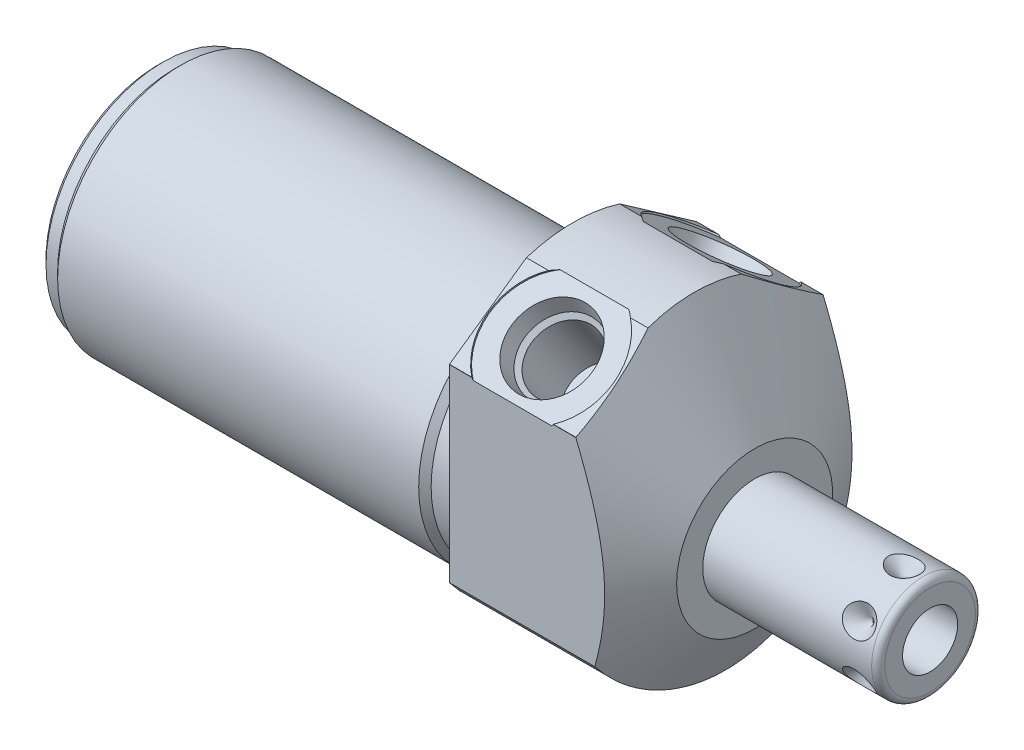
SolidWorks part; units mm, degrees
material "Alloy Steel"
ref_plane "Front Plane" through (0, 0, 0) normal (0, 0, 1) x (1, 0, 0)
ref_plane "Top Plane" through (0, 0, 0) normal (0, 1, 0) x (1, 0, 0)
ref_plane "Right Plane" through (0, 0, 0) normal (1, 0, 0) x (0, 0, -1)
ref_plane "Plane1" through (0, 0, 0) normal (1, 0, 0) x (0, 0, -1)
sketch "Sketch1" plane through (0, 0, 0) normal (1, 0, 0) x (0, 0, -1)
  circle A0 centre (0, 0) radius 23.8125
  dimension "D1" = 47.625
extrude "Extrude1" add sketch "Sketch1" along normal blind 27.7876 and the other way blind 63.5
ref_plane "Plane2" through (0, 0, 0) normal (1, 0, 0) x (0, 0, -1)
sketch "Sketch2" plane through (0, 0, 0) normal (1, 0, 0) x (0, 0, -1)
  line L0 (-20.7455, -4.191) -> (20.7455, -4.191) construction
  circle A0 centre (0, -4.191) radius 18.8595
  circle A1 centre (0, 0) radius 23.8125 construction
  circle A2 centre (0, 0) radius 23.8125
  dimension "D2" = 37.719
  dimension "D1" = 4.191
extrude "Cut-Extrude1" cut sketch "Sketch2" against normal up to next
ref_plane "Plane4" through (0, 0, 0) normal (-1, 0, 0) x (0, 0, 1)
sketch "Sketch4" plane through (0, 0, 0) normal (-1, 0, 0) x (0, 0, 1)
  line L0 (18.923, -14.4553) -> (18.923, 14.4659)
  line L1 (18.923, 14.4659) -> (0, 27.7159)
  line L2 (-18.923, -14.4553) -> (-18.923, 14.4659)
  line L3 (-18.923, 14.4659) -> (0, 27.7159)
  line L4 (0, -26.3889) -> (0, 30.2923) construction
  circle A0 centre (0, 0) radius 28.575
  circle A1 centre (0, 0) radius 23.8125 construction
  arc A3 (-18.923, -14.4553) -> (18.923, -14.4553) centre (0, 0) ccw
  dimension "D4" = 57.15
  dimension "D1" = 37.846
  dimension "D2" = 27.7159
  dimension "D3" = 55
extrude "Cut-Extrude3" cut sketch "Sketch4" against normal up to next
ref_plane "Plane6" through (0, 0, 0) normal (0, 0, 1) x (1, 0, 0)
sketch "Sketch6" plane through (0, 0, 0) normal (0, 0, 1) x (1, 0, 0)
  line L0 (4.764, 47.625) -> (27.7876, 7.747)
  line L1 (3.6128, -4.191) -> (28.9388, -4.191) construction
  line L2 (-63.5, -4.191) -> (0, -4.191) construction
  line L3 (27.7876, 7.747) -> (27.7876, 47.625)
  line L4 (27.7876, 47.625) -> (4.764, 47.625)
  line L5 (27.7876, -14.4553) -> (27.7876, 14.4553) construction
  dimension "D1" = 23.876
  dimension "D2" = 30
  dimension "D3" = 39.878
revolve "Cut-Revolve2" cut sketch "Sketch6" angle 360 about L1
ref_plane "Plane7" through (9.652, 18.3948, 12.869) normal (1, 0, 0) x (0, 0.5736, -0.8192)
sketch "S2D0002" plane through (9.652, 18.3948, 12.869) normal (1, 0, 0) x (0, 0.5736, -0.8192)
  line L0 (0, 0) -> (6.1849, 0)
  line L1 (6.1849, 0) -> (5.6423, -2.5527)
  line L2 (5.6423, -2.5527) -> (4.9784, -3.2166)
  line L3 (4.9784, -3.2166) -> (4.9784, -13.462)
  line L4 (4.9784, -13.462) -> (0, -13.462)
  line L5 (0, -13.462) -> (0, 0)
  line L6 (0, -14.1351) -> (0, 0.6731) construction
  dimension "D1" = 13.462
revolve "Cut-Revolve3" cut sketch "S2D0002" angle 360 about L6
ref_plane "Plane8" through (9.652, 18.3948, -12.869) normal (1, 0, 0) x (0, -0.5736, -0.8192)
sketch "Sketch8" plane through (9.652, 18.3948, -12.869) normal (1, 0, 0) x (0, -0.5736, -0.8192)
  line L0 (0, 0) -> (6.1849, 0)
  line L1 (6.1849, 0) -> (5.6423, -2.5527)
  line L2 (5.6423, -2.5527) -> (4.9784, -3.2166)
  line L3 (4.9784, -3.2166) -> (4.9784, -13.462)
  line L4 (4.9784, -13.462) -> (0, -13.462)
  line L5 (0, -13.462) -> (0, 0)
  line L6 (0, -14.1351) -> (0, 0.6731) construction
  dimension "D1" = 13.462
revolve "Cut-Revolve4" cut sketch "Sketch8" angle 360 about L6
sketch "Sketch18" plane through (0, 18.5976, 13.0222) normal (0, 0.8192, 0.5736) x (1, 0, 0)
  circle A0 centre (9.652, 0.0091) radius 9.525
  dimension "D1" = 19.05
extrude "Cut-Extrude4" cut sketch "Sketch18" against normal blind 0.254
sketch "Sketch19" plane through (0, 18.5976, -13.0222) normal (0, 0.8192, -0.5736) x (1, 0, 0)
  circle A0 centre (9.652, -0.0091) radius 9.525
  dimension "D1" = 19.05
extrude "Cut-Extrude5" cut sketch "Sketch19" against normal blind 0.254
ref_plane "Plane10" through (0, 0, 0) normal (0, 0, 1) x (1, 0, 0)
sketch "Sketch10" plane through (0, 0, 0) normal (0, 0, 1) x (1, 0, 0)
  line L0 (0, 14.6685) -> (0, 13.716)
  line L1 (0, 13.716) -> (-3.81, 13.716)
  line L2 (-3.81, 13.716) -> (-4.7625, 14.6685)
  line L3 (-5.0006, -4.191) -> (0.2381, -4.191) construction
  line L4 (0, 14.6685) -> (-4.7625, 14.6685)
  line L5 (-63.5, -4.191) -> (0, -4.191) construction
  line L6 (0, 14.6685) -> (-63.5, 14.6685) construction
  line L7 (0, 14.6685) -> (0, -23.0505) construction
  dimension "D1" = 35.814
  dimension "D2" = 3.81
  dimension "D3" = 45
revolve "Cut-Revolve6" cut sketch "Sketch10" angle 360 about L3
ref_plane "Plane12" through (0, 0, 0) normal (0, 0, 1) x (1, 0, 0)
sketch "Sketch12" plane through (0, 0, 0) normal (0, 0, 1) x (1, 0, 0)
  line L0 (-63.5, 14.6685) -> (-63.5, 13.716)
  line L1 (-63.5, 13.716) -> (-60.96, 13.716)
  line L2 (-60.96, 13.716) -> (-60.0075, 14.6685)
  line L3 (-63.6746, -4.191) -> (-59.8329, -4.191) construction
  line L4 (-63.5, 14.6685) -> (-60.0075, 14.6685)
  line L6 (-63.5, -4.191) -> (-4.7625, -4.191) construction
  line L7 (-4.7625, 14.6685) -> (-63.5, 14.6685) construction
  line L8 (-63.5, 14.6685) -> (-63.5, -23.0505) construction
  dimension "D1" = 35.814
  dimension "D2" = 2.54
  dimension "D3" = 45
revolve "Cut-Revolve8" cut sketch "Sketch12" angle 360 about L3
chamfer "Chamfer1" distance 0.762 angle 45 1 edges at (-63.5, -4.191, 17.907)
ref_plane "Plane13" through (0, 0, 0) normal (0, 0, 1) x (0, -1, 0)
sketch "Sketch13" plane through (0, 0, 0) normal (0, 0, 1) x (0, -1, 0)
  line L0 (4.191, 27.7876) -> (4.191, 54.6354)
  line L1 (4.191, 54.6354) -> (11.1125, 54.6354)
  line L2 (12.1285, 53.6194) -> (12.1285, 27.7876)
  line L3 (12.1285, 27.7876) -> (4.191, 27.7876)
  line L4 (4.191, 26.4452) -> (4.191, 55.9778) construction
  line L5 (4.191, -60.0075) -> (4.191, -4.7625) construction
  line L6 (16.129, 27.7876) -> (-7.747, 27.7876) construction
  line L7 (14.4553, 0) -> (-14.4553, 0) construction
  arc A0 (12.1285, 53.6194) -> (11.1125, 54.6354) centre (11.1125, 53.6194) ccw
  dimension "D2" = 1.016
  dimension "D1" = 54.6354
  dimension "D3" = 15.875
revolve "Revolve1" add sketch "Sketch13" angle 360 about L4
ref_plane "Plane14" through (54.6354, -8.4074, 0) normal (0, 0, 1) x (0, -1, 0)
sketch "S2D0001" plane through (54.6354, -8.4074, 0) normal (0, 0, 1) x (0, -1, 0)
  line L0 (0, 0) -> (0, -15.24)
  line L1 (0, -15.24) -> (-4.2164, -17.7735)
  line L2 (0, 0) -> (-4.2164, 0)
  line L3 (-4.2164, 0) -> (-4.2164, -17.7735)
  line L4 (-4.2164, -18.6621) -> (-4.2164, 0.8887) construction
  line L5 (-4.2164, -1.016) -> (-4.2164, -26.8478) construction
  line L6 (2.7051, 0) -> (-11.1379, 0) construction
  dimension "D1" = 8.4328
  dimension "D2" = 15.24
  dimension "D3" = 59
revolve "Cut-Revolve9" cut sketch "S2D0001" angle 360 about L4
ref_plane "Plane16" through (50.673, -12.1285, 0) normal (0, 0, 1) x (-1, 0, 0)
ref_plane "Plane17" through (0, -3.1433, -1.8148) normal (0, 0.866, 0.5) x (-1, 0, 0)
sketch "Sketch16" plane through (50.673, 3.7465, 0) normal (0, 0, -1) x (-1, 0, 0)
  line L0 (0, 0) -> (2.413, 0)
  line L1 (2.413, 0) -> (0, -2.413)
  line L2 (0, 0) -> (0, -2.413)
  line L3 (0, -5.071) -> (0, 0.1207) construction
  line L4 (-3.9624, -1.016) -> (-3.9624, -14.859) construction
  line L5 (22.8854, 0) -> (-2.9464, 0) construction
  dimension "D1" = 3.9624
  dimension "D2" = 4.826
  dimension "D3" = 45
revolve "Cut-Revolve10" cut sketch "Sketch16" angle 360 about L3
pattern_circular "CirPattern1" count 6 over 360 about axis through (26.4452, -4.191, 0) along (-1, 0, 0) of "Cut-Revolve10"
